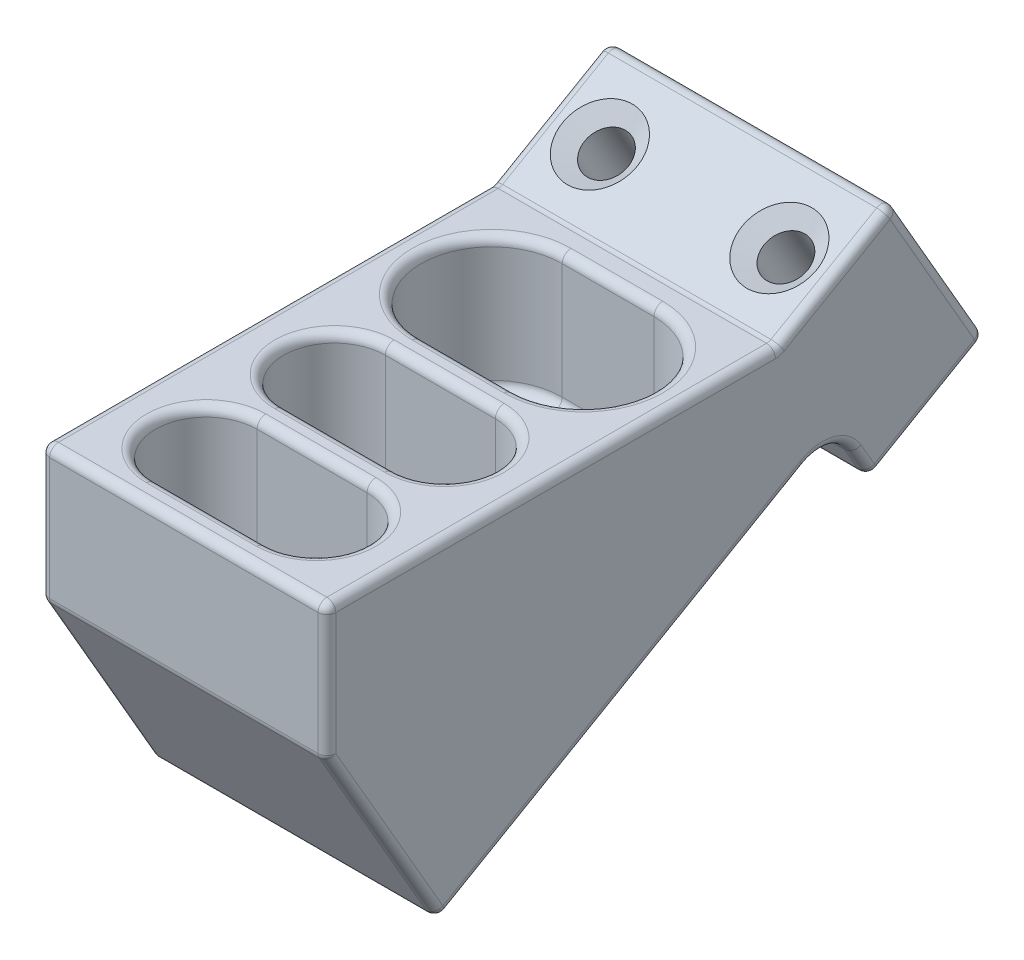
SolidWorks part; units mm, degrees
ref_plane "Front Plane" through (0, 0, 0) normal (0, 0, 1) x (1, 0, 0)
ref_plane "Top Plane" through (0, 0, 0) normal (0, 1, 0) x (1, 0, 0)
ref_plane "Right Plane" through (0, 0, 0) normal (1, 0, 0) x (0, 0, -1)
sketch "Sketch1" plane through (0, 0, 0) normal (0, 1, 0) x (1, 0, 0)
  line L0 (0, 0) -> (0, -31.0825) construction
  line L1 (-5.1594, 0) -> (5.1594, 0) construction
  line L2 (-5.1594, 7.9375) -> (5.1594, 7.9375)
  line L3 (-5.1594, -7.9375) -> (5.1594, -7.9375)
  line L4 (-6.1912, -16.6525) -> (6.1913, -16.6525) construction
  line L5 (-6.1912, -10.9375) -> (6.1913, -10.9375)
  line L6 (-6.1912, -22.3675) -> (6.1913, -22.3675)
  line L7 (-6.1912, -31.0825) -> (6.1913, -31.0825) construction
  line L8 (-6.1912, -25.3675) -> (6.1913, -25.3675)
  line L9 (-6.1912, -36.7975) -> (6.1913, -36.7975)
  line L10 (6.1913, -22.3675) -> (6.1913, -25.3675) construction
  line L11 (6.1913, -10.9375) -> (6.1912, -7.9375) construction
  line L12 (-16.0969, 10.9375) -> (-16.0969, -39.7975)
  line L17 (-13.0969, 7.9375) -> (13.0969, 7.9375) construction
  line L18 (-13.0969, 7.9375) -> (-13.0969, -36.7975) construction
  line L19 (-13.0969, -36.7975) -> (13.0969, -36.7975) construction
  line L20 (13.0969, 7.9375) -> (13.0969, -36.7975) construction
  line L21 (-16.0969, -39.7975) -> (16.0969, -39.7975)
  line L22 (16.0969, 10.9375) -> (16.0969, -39.7975)
  line L23 (-16.0969, 10.9375) -> (16.0969, 10.9375)
  arc A0 (-5.1594, 7.9375) -> (-5.1594, -7.9375) centre (-5.1594, 0) ccw
  arc A1 (5.1594, -7.9375) -> (5.1594, 7.9375) centre (5.1594, 0) ccw
  arc A2 (-6.1912, -10.9375) -> (-6.1912, -22.3675) centre (-6.1912, -16.6525) ccw
  arc A3 (6.1913, -22.3675) -> (6.1913, -10.9375) centre (6.1913, -16.6525) ccw
  arc A4 (-6.1912, -25.3675) -> (-6.1912, -36.7975) centre (-6.1912, -31.0825) ccw
  arc A5 (6.1913, -36.7975) -> (6.1913, -25.3675) centre (6.1913, -31.0825) ccw
  point P5 (0, 0)
  point P10 (0, -16.6525)
  point P17 (13.0969, 0)
  point P18 (-13.0969, 0)
  point P19 (11.9063, -16.6525)
  point P20 (-11.9062, -16.6525)
  point P21 (0, -31.0825)
  dimension "D1" = 26.1937
  dimension "D2" = 15.875
  dimension "D3" = 23.8125
  dimension "D4" = 11.43
  dimension "D5" = 3
  dimension "D6" = 3
extrude "Boss-Extrude1" add sketch "Sketch1" against normal blind 15
sketch "Sketch2" plane through (0, 0, 0) normal (1, 0, 0) x (0, 0, -1)
  line L0 (-39.7975, -15) -> (-27.1138, -36.9689)
  line L1 (21.4327, -18.1782) -> (34.4231, -10.6782)
  line L2 (34.4231, -10.6782) -> (23.9279, 7.5)
  line L3 (23.9279, 7.5) -> (10.9375, 0)
  line L4 (-39.7975, -15) -> (10.9375, -15)
  line L5 (10.9375, -15) -> (10.9375, 0)
  line L6 (-39.7975, 0) -> (10.9375, 0) construction
  line L7 (-27.1138, -36.9689) -> (17.4327, -11.25)
  line L8 (17.4327, -11.25) -> (21.4327, -18.1782)
  line L9 (-27.1138, -36.9689) -> (-23.1138, -43.8971) construction
  line L10 (-23.1138, -43.8971) -> (21.4327, -18.1782) construction
  dimension "D1" = 150
  dimension "D2" = 15
  dimension "D3" = 8
extrude "Boss-Extrude2" add sketch "Sketch2" along normal up to surface (32.1938 mm away) from surface at -16.0969 contours L0 L7 L4 | L7 L8 L1 L2 L3 L5 up to face at (16.0969, -7.5, 14.43) starting at face at (-16.0969, -7.5, 14.43)
fillet "Fillet2" radius 4 1 edges at (0, -11.25, -17.4327)
fillet "Fillet1" radius 1 37 edges at (0, 0, -10.9375) (16.0969, -25.9844, 33.4556) (-16.0969, -25.9844, 33.4556) (16.0969, 3.75, -17.4327) (-16.0969, 3.75, -17.4327) (0, 7.5, -23.9279) (16.0969, -1.5891, -29.1755) (-16.0969, -1.5891, -29.1755) (0, -10.6782, -34.4231) (16.0969, -14.4282, -27.9279) (-16.0969, -14.4282, -27.9279) (-11.9062, 0, 31.0825) (0, 0, 36.7975) (11.9063, 0, 31.0825) (0, 0, 25.3675) (-11.9063, 0, 16.6525) (0, 0, 22.3675) (11.9063, 0, 16.6525) (0, 0, 10.9375) (0, 0, 7.9375) (13.0969, 0, 0) (0, 0, -7.9375) (-16.0969, 0, 14.43) (0, 0, 39.7975) (16.0969, 0, 14.43) (0, -15, 39.7975) (-16.0969, -7.5, 39.7975) (16.0969, -7.5, 39.7975) (-13.0969, 0, 0) (16.0969, -16.4462, -20.4327) (-16.0969, -16.4462, -20.4327) (0, -18.1782, -21.4327) (-16.0969, -25.1094, 6.5726) (16.0969, -25.1094, 6.5726) (0, -36.9689, 27.1138) (-16.0969, -12.8504, -17.0039) (16.0969, -12.8504, -17.0039)
sketch "Sketch3" plane through (0, -4.7361, -2.7344) normal (0, 0.866, 0.5) x (1, 0, 0)
  line L0 (-15.0969, 16.6061) -> (-10.0969, 16.6061) construction
  line L2 (15.0969, 16.6061) -> (10.0969, 16.6061) construction
  line L3 (15.0969, 9.7401) -> (15.0969, 23.4722) construction
  line L4 (-15.0969, 23.4722) -> (-15.0969, 9.7401) construction
  dimension "D1" = 5
hole_wizard "CSK for #8 Flat Head Machine Screw (100)1" positions "3DSketch1" profile "Sketch4" countersink size "#8" standard "ANSI Inch" end condition through all
sketch3d "3DSketch1"
  point P0 (-10.0969, 3.567, -17.1157)
  point P3 (10.0969, 3.567, -17.1157)
sketch "Sketch4" plane through (-10.0969, 3.567, -17.1157) normal (1, 0, 0) x (0, -0.5, 0.866)
  line L0 (0, 0) -> (0, 43.2588)
  line L1 (0, 43.2588) -> (2.4574, 43.2588)
  line L2 (2.4574, 43.2588) -> (2.4574, 1.4759)
  line L3 (2.4574, 1.4759) -> (4.2164, 0)
  line L5 (4.2164, 0) -> (0, 0)
  line L6 (-2.4574, 1.4759) -> (-4.2164, 0) construction
  line L11 (0, -6.35) -> (0, 107.95) construction
  dimension "Thru Hole Dia." = 4.9149
  dimension "Thru Hole Depth" = 43.2588
  dimension "Near C'Sink Dia." = 8.4328
  dimension "Near C'Sink Angle" = 100
fillet "Fillet3" radius 1 12 edges at (11.9063, -15, 31.0825) (0, -15, 36.7975) (-11.9062, -15, 31.0825) (0, -15, 25.3675) (11.9063, -15, 16.6525) (0, -15, 22.3675) (-11.9063, -15, 16.6525) (0, -15, 10.9375) (13.0969, -15, 0) (0, -15, 7.9375) (-13.0969, -15, 0) (0, -15, -7.9375)
